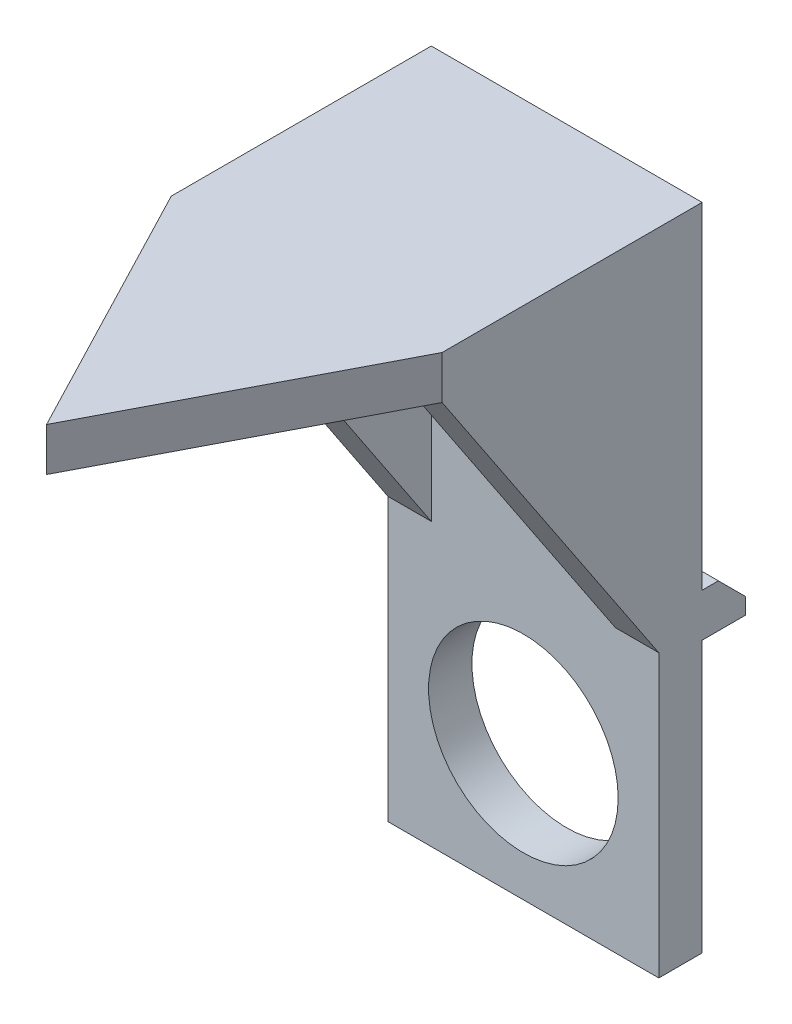
SolidWorks part; units mm, degrees
material "ABS"
ref_plane "Front Plane" through (0, 0, 0) normal (0, 0, 1) x (1, 0, 0)
ref_plane "Top Plane" through (0, 0, 0) normal (0, 1, 0) x (1, 0, 0)
ref_plane "Right Plane" through (0, 0, 0) normal (1, 0, 0) x (0, 0, -1)
sketch "Sketch1" plane through (0, 0, 0) normal (0, 0, 1) x (1, 0, 0)
  line L1 (-5, 19) -> (5, 19)
  line L2 (-5, 19) -> (-5, -5)
  line L3 (-5, -5) -> (5, -5)
  line L4 (5, 19) -> (5, -5)
  dimension "D1" = 5
  dimension "D2" = 24
  dimension "D3" = 5
  dimension "D4" = 5
extrude "Body" add sketch "Sketch1" along normal blind 1.6
sketch "Sketch2" plane through (0, 0, 0) normal (0, 0, -1) x (-1, 0, 0)
  line L0 (-5, -5) -> (-5, 19) construction
  line L1 (-5, 6.6) -> (5, 6.6)
  line L2 (-5, 6.6) -> (-5, 5)
  line L3 (-5, 5) -> (5, 5)
  line L4 (5, 6.6) -> (5, 5)
  line L5 (5, 19) -> (5, -5) construction
  line L6 (5, -5) -> (-5, -5) construction
  dimension "D1" = 1.6
  dimension "D2" = 10
extrude "Boss-Extrude2" add sketch "Sketch2" along normal blind 1.6
chamfer "Fin Chamfer" distance 1 angle 45 1 edges at (0, 6.6, -1.6)
sketch "Sketch3" plane through (0, 0, 1.6) normal (0, 0, 1) x (1, 0, 0)
  circle A0 centre (0, 0) radius 3.5
  dimension "D1" = 7
extrude "Hole" cut sketch "Sketch3" against normal through all
sketch "Sketch4" plane through (0, 0, 1.6) normal (0, 0, 1) x (1, 0, 0)
  line L0 (-5, 19) -> (-5, 5.4)
  line L1 (-5, 19) -> (-5, -5) construction
  line L2 (-5, 5.4) -> (-3.4, 5.4)
  line L3 (-3.4, 5.4) -> (-3.4, 17.4)
  line L4 (-3.4, 17.4) -> (3.4, 17.4)
  line L5 (3.4, 17.4) -> (3.4, 5.4)
  line L6 (3.4, 5.4) -> (5, 5.4)
  line L7 (5, -5) -> (5, 19) construction
  line L8 (5, 5.4) -> (5, 19)
  line L9 (5, 19) -> (-5, 19) construction
  line L10 (5, 19) -> (-5, 19)
  dimension "D1" = 1.6
  dimension "D2" = 1.6
  dimension "D3" = 1.6
  dimension "D4" = 13.6
  dimension "D5" = 13.6
extrude "Fin" add sketch "Sketch4" along normal blind 17.6049
sketch "Sketch5" plane through (5, 0, 0) normal (1, 0, 0) x (0, 0, -1)
  line L0 (-1.6, 5.4) -> (-9.6, 5.4)
  line L1 (-19.2049, 5.4) -> (-1.6, 5.4) construction
  line L3 (-9.6, 17.4) -> (-1.6, 5.4)
  line L6 (-9.6, 17.4) -> (-19.2049, 17.4)
  line L7 (-19.2049, 17.4) -> (-19.2049, 5.4)
  line L8 (-19.2049, 5.4) -> (-19.2049, 19) construction
  line L9 (-19.2049, 5.4) -> (-9.6, 5.4)
  dimension "D2" = 12
extrude "Side Cut" cut sketch "Sketch5" against normal through all
sketch "Sketch7" plane through (0, 17.4, 0) normal (0, -1, 0) x (1, 0, 0)
  line L0 (-5, 9.6) -> (0, 19.2049)
  line L1 (-5, 19.2049) -> (5, 19.2049) construction
  line L2 (0, 19.2049) -> (5, 9.6)
  line L3 (5, 9.6) -> (5, 19.2049)
  line L4 (-5, 19.2049) -> (0, 19.2049)
  line L5 (-5, 19.2049) -> (-5, 9.6)
  line L6 (0, 19.2049) -> (5, 19.2049)
  line M5 (5, 9.6) -> (5, 19.2049)
  line M6 (5, 19.2049) -> (-5, 19.2049)
  line M7 (-5, 19.2049) -> (-5, 9.6)
  dimension "D1" = 55
extrude "Top Cut" cut sketch "Sketch7" against normal through all contours L0 M7 M6 | L2 M6 M5
